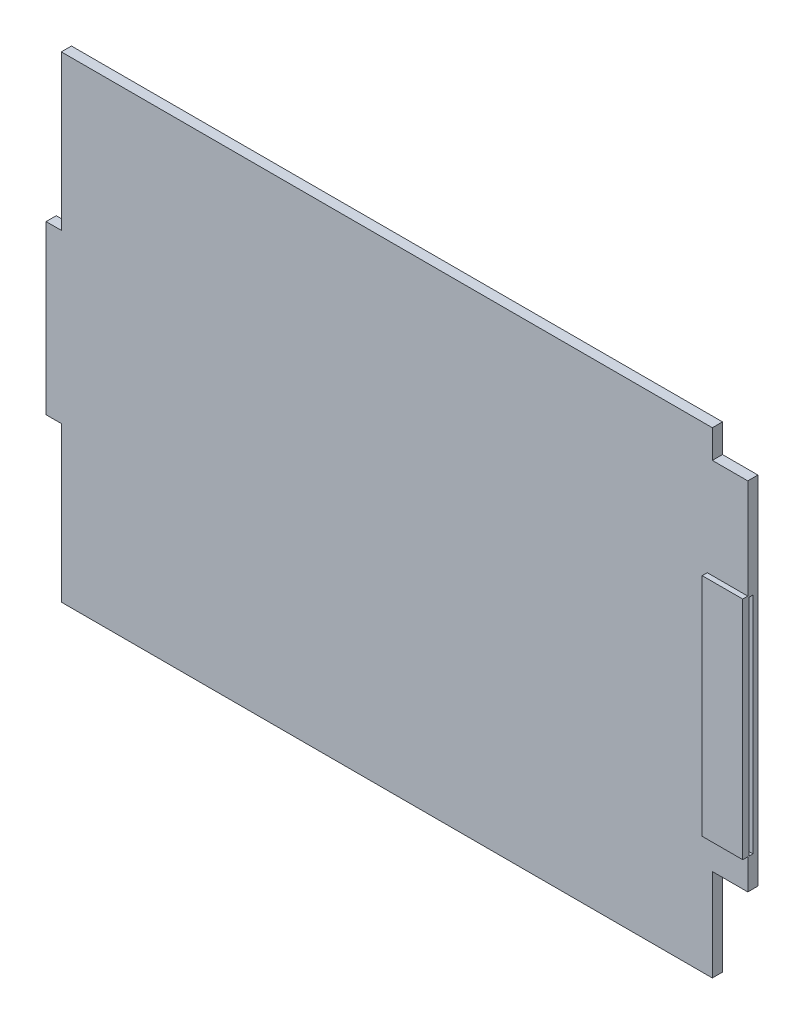
SolidWorks part; units mm, degrees
material "VITON"
ref_plane "Plan de face" through (0, 0, 0) normal (0, 0, 1) x (1, 0, 0)
ref_plane "Plan de dessus" through (0, 0, 0) normal (0, 1, 0) x (1, 0, 0)
ref_plane "Plan de droite" through (0, 0, 0) normal (1, 0, 0) x (0, 0, -1)
sketch "Esquisse1" plane through (0, 0, 0) normal (0, 0, 1) x (1, 0, 0)
  line L0 (34.6, 20.7065) -> (31.1043, 20.7065)
  line L1 (31.1043, 20.7065) -> (31.1043, 23.4978)
  line L2 (31.1043, 23.4978) -> (-33.0954, 23.4978)
  line L3 (-33.0954, 23.4978) -> (-33.0954, 8.2522)
  line L4 (-33.0954, 8.2522) -> (-34.5108, 8.2522)
  line L5 (-34.5108, 8.2522) -> (-34.6, 8.2522)
  line L6 (-34.6, 8.2522) -> (-34.6, -8.2478)
  line L7 (-34.6, -8.2478) -> (-33.0954, -8.2478)
  line L8 (-33.0954, -8.2478) -> (-33.0954, -23.4978)
  line L9 (-33.0954, -23.4978) -> (31.1043, -23.4978)
  line L10 (31.1043, -23.4978) -> (31.1043, -14.4021)
  line L11 (31.1043, -14.4021) -> (34.6, -14.4021)
  line L12 (34.6, -14.4021) -> (34.6, 20.7065)
extrude "Boss.-Extru.1" add sketch "Esquisse1" along normal blind 1
sketch "Esquisse2" plane through (0, 0, 1) normal (0, 0, 1) x (1, 0, 0)
  line L0 (34.6, 20.7065) -> (34.6, 10.7026) construction
  line L1 (34.6, -14.4021) -> (34.6, 20.7065) construction
  line L2 (34.6, -14.4021) -> (34.6, -11.3979) construction
  line L4 (34.6, 10.7026) -> (30.6, 10.7026)
  line L5 (34.6, 10.7026) -> (34.6, -11.3979)
  line L6 (34.6, -11.3979) -> (30.6, -11.3979)
  line L7 (30.6, 10.7026) -> (30.6, -11.3979)
  dimension "D1" = 4
extrude "Enlèv. mat.-Extru.2" cut sketch "Esquisse2" against normal blind 0.5
sketch "Esquisse3" plane through (0, 0, 1) normal (0, 0, 1) x (1, 0, 0)
  line L0 (30.6, 10.7026) -> (30.6, -11.3979) construction
  line L1 (30.6, -11.3979) -> (34.6, -11.3979)
  line L2 (30.6, -11.3979) -> (30.6, 10.8649)
  line L3 (30.6, 10.8649) -> (34.6, 10.8649)
  line L4 (34.6, -11.3979) -> (34.6, 10.8649)
  line L5 (34.6, 10.7026) -> (34.6, 20.7065) construction
extrude "Boss.-Extru.2" add sketch "Esquisse3" along normal blind 0.5 and the other way blind 0.1
